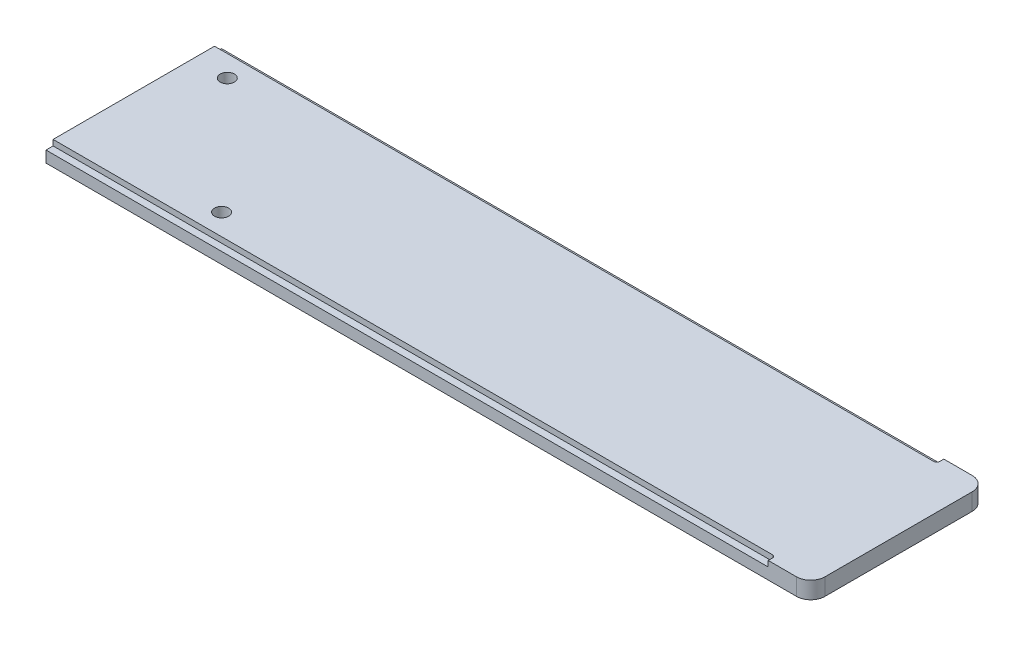
SolidWorks part; units mm, degrees
material "Acrylic (Medium-high impact)"
ref_plane "Front Plane" through (0, 0, 0) normal (0, 0, 1) x (1, 0, 0)
ref_plane "Top Plane" through (0, 0, 0) normal (0, 1, 0) x (1, 0, 0)
ref_plane "Right Plane" through (0, 0, 0) normal (1, 0, 0) x (0, 0, -1)
sketch "Sketch1" plane through (0, 0, 0) normal (0, 1, 0) x (1, 0, 0)
  line L1 (0, 0) -> (270, 0)
  line L2 (0, 0) -> (0, 62)
  line L3 (0, 62) -> (270, 62)
  line L4 (270, 0) -> (270, 62)
  dimension "D1" = 270
  dimension "D2" = 62
extrude "Boss-Extrude1" add sketch "Sketch1" along normal blind 6
sketch "Sketch2" plane through (0, 6, 0) normal (0, 1, 0) x (1, 0, 0)
  line L0 (270, 0) -> (270, 62) construction
  line L1 (0, 62) -> (255, 62)
  line L2 (0, 62) -> (0, 59.5)
  line L3 (0, 59.5) -> (255, 59.5)
  line L4 (255, 62) -> (255, 59.5)
  line L5 (0, 0) -> (255, 0)
  line L6 (0, 0) -> (0, 2.5)
  line L7 (0, 2.5) -> (255, 2.5)
  line L8 (255, 0) -> (255, 2.5)
  dimension "D1" = 2.5
  dimension "D2" = 2.5
  dimension "D3" = 15
  dimension "D4" = 15
extrude "Cut-Extrude1" cut sketch "Sketch2" against normal blind 2
fillet "Fillet1" radius 1 2 edges at (255, 5, -2.5) (255, 5, -59.5)
sketch "Sketch3" plane through (0, 6, 0) normal (0, 1, 0) x (1, 0, 0)
  line L0 (0, 59.5) -> (0, 2.5) construction
  circle A0 centre (12, 52) radius 2.5
  circle A1 centre (52, 10) radius 2.5
  dimension "D1" = 5
  dimension "D2" = 5
  dimension "D3" = 12
  dimension "D4" = 52
  dimension "D5" = 10
  dimension "D6" = 10
extrude "Cut-Extrude2" cut sketch "Sketch3" against normal through all
fillet "Fillet2" radius 5 2 edges at (270, 3, -62) (270, 3, 0)
